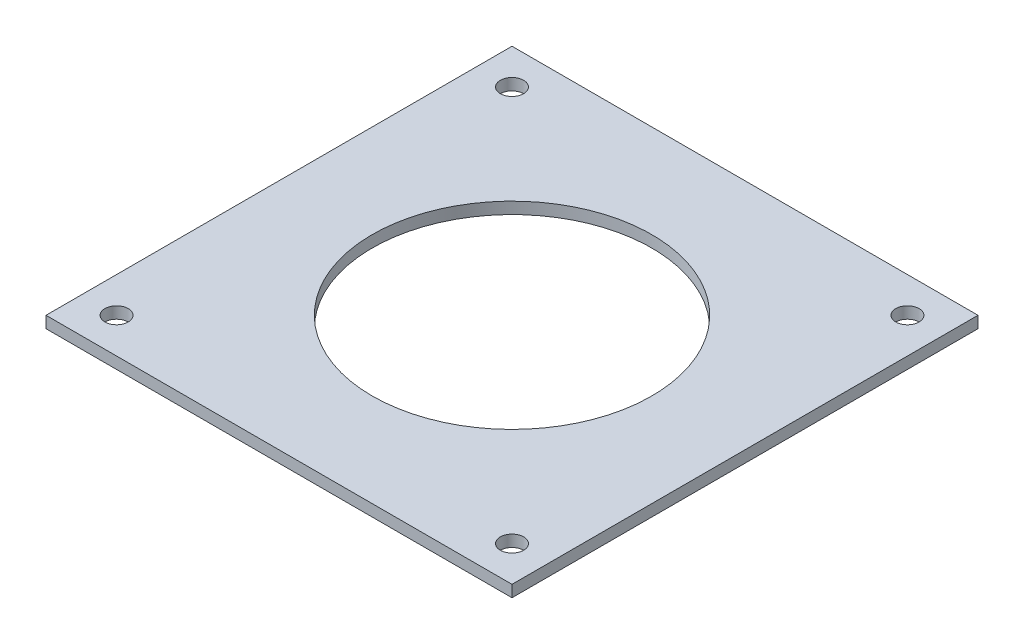
SolidWorks part; units mm, degrees
ref_plane "Front Plane" through (0, 0, 0) normal (0, 0, 1) x (1, 0, 0)
ref_plane "Top Plane" through (0, 0, 0) normal (0, 1, 0) x (1, 0, 0)
ref_plane "Right Plane" through (0, 0, 0) normal (1, 0, 0) x (0, 0, -1)
sketch "Sketch1" plane through (0, 0, 0) normal (0, 1, 0) x (1, 0, 0)
  line L1 (63.5, -63.5) -> (-63.5, -63.5)
  line L2 (63.5, -63.5) -> (63.5, 63.5)
  line L3 (63.5, 63.5) -> (-63.5, 63.5)
  line L4 (-63.5, -63.5) -> (-63.5, 63.5)
  line L5 (63.5, -63.5) -> (-63.5, 63.5) construction
  line L6 (63.5, 63.5) -> (-63.5, -63.5) construction
  circle A1 centre (0, 0) radius 38.1
  circle A2 centre (-53.8815, 53.8815) radius 3.175
  circle A6 centre (53.8815, 53.8815) radius 3.175
  circle A7 centre (53.8815, -53.8815) radius 3.175
  circle A8 centre (-53.8815, -53.8815) radius 3.175
  point P15 (0, 0)
  point P19 (0, 0)
  dimension "D1" = 76.2
  dimension "D2" = 127
  dimension "D3" = 6.35
  dimension "D5" = 4
  dimension "D4" = 76.2
extrude "Boss-Extrude1" add sketch "Sketch1" along normal blind 3.175
